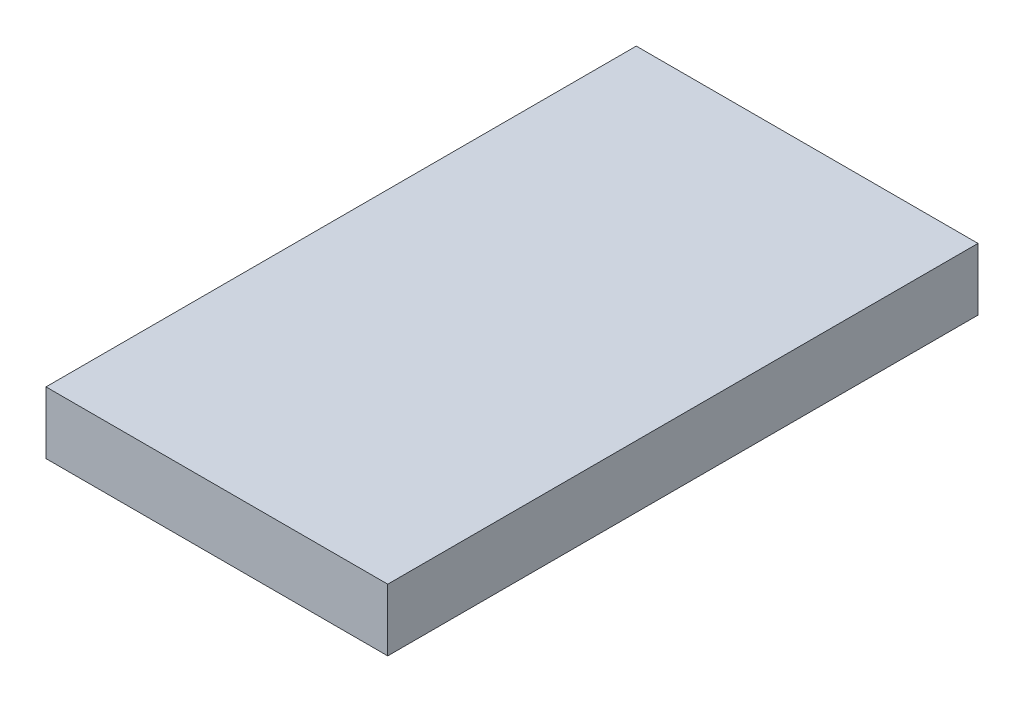
SolidWorks part; units mm, degrees
ref_plane "Front Plane" through (0, 0, 0) normal (0, 0, 1) x (1, 0, 0)
ref_plane "Top Plane" through (0, 0, 0) normal (0, 1, 0) x (1, 0, 0)
ref_plane "Right Plane" through (0, 0, 0) normal (1, 0, 0) x (0, 0, -1)
sketch "Sketch1" plane through (0, 0, 0) normal (0, 1, 0) x (1, 0, 0)
  line L1 (-13.75, 23.75) -> (13.75, 23.75)
  line L2 (-13.75, 23.75) -> (-13.75, -23.75)
  line L3 (-13.75, -23.75) -> (13.75, -23.75)
  line L4 (13.75, 23.75) -> (13.75, -23.75)
  line L5 (-13.75, 23.75) -> (13.75, -23.75) construction
  line L6 (-13.75, -23.75) -> (13.75, 23.75) construction
  point P0 (0, 0)
  point P6 (0, 0)
  dimension "D1" = 47.5
  dimension "D2" = 27.5
extrude "Boss-Extrude1" add sketch "Sketch1" along normal blind 5
